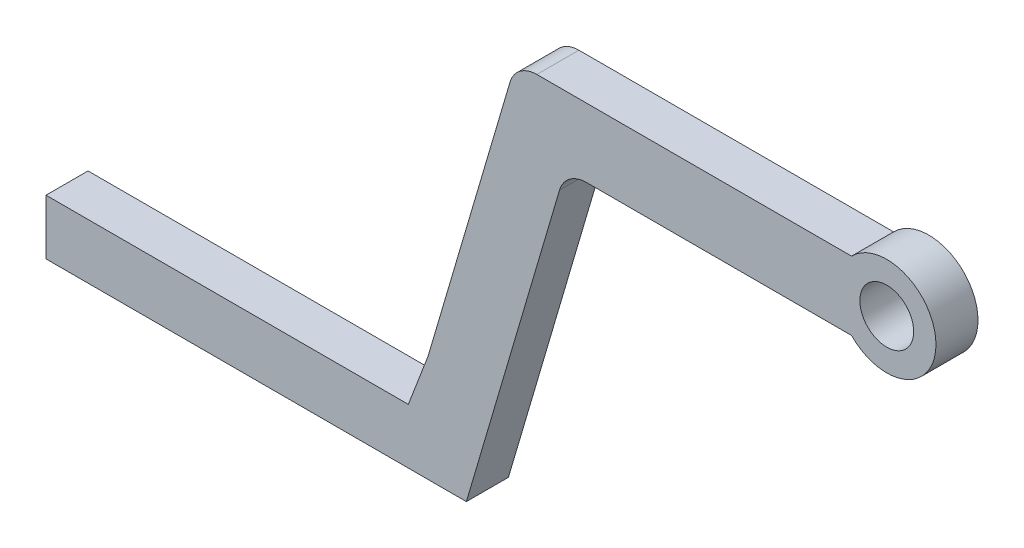
SolidWorks part; units mm, degrees
ref_plane "Front Plane" through (0, 0, 0) normal (0, 0, 1) x (1, 0, 0)
ref_plane "Top Plane" through (0, 0, 0) normal (0, 1, 0) x (1, 0, 0)
ref_plane "Right Plane" through (0, 0, 0) normal (1, 0, 0) x (0, 0, -1)
sketch "Sketch1" plane through (0, 0, 0) normal (0, 0, 1) x (1, 0, 0)
  line L0 (0, 30.4953) -> (0, 36.7226)
  line L1 (0, 36.7226) -> (-33.6108, 36.7226)
  line L2 (-33.6108, 36.7226) -> (-41.5757, 9.6694)
  line L3 (0, 30.4953) -> (-29.1216, 30.4953)
  line L4 (-29.1216, 30.4953) -> (-38.1, 0)
  line L5 (-38.1, 0) -> (-76.2, 0)
  line L6 (-76.2, 0) -> (-76.2, 5.0027)
  line L7 (-76.2, 5.0027) -> (-43.362, 5.0027)
  line L8 (-43.362, 5.0027) -> (-41.5757, 9.6694)
extrude "Boss-Extrude1" add sketch "Sketch1" along normal blind 3.81
sketch "Sketch2" plane through (0, 0, 3.81) normal (0, 0, 1) x (1, 0, 0)
  line L0 (0, 30.4953) -> (0, 36.7226) construction
  circle A0 centre (0, 33.6089) radius 4.459
extrude "Boss-Extrude2" add sketch "Sketch2" against normal blind 3.81 contours A0
sketch "Sketch3" plane through (0, 0, 3.81) normal (0, 0, 1) x (1, 0, 0)
  circle A0 centre (0, 33.6089) radius 2.4377
extrude "Cut-Extrude1" cut sketch "Sketch3" against normal blind 5.08
fillet "Fillet1" radius 2.54 1 edges at (-33.6108, 36.7226, 1.905)
fillet "Fillet2" radius 2.54 1 edges at (-29.1216, 30.4953, 1.905)
